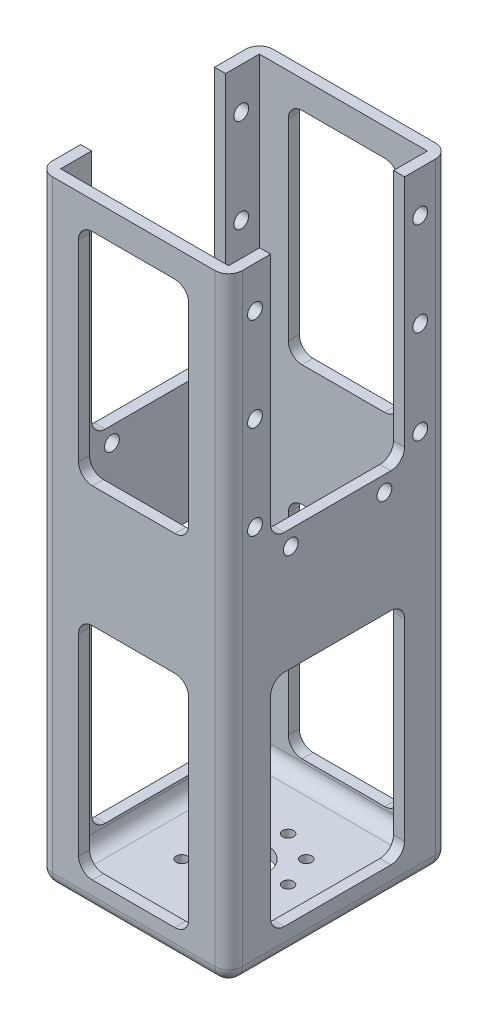
SolidWorks part; units mm, degrees
material "PLA"
ref_plane "Front Plane" through (0, 0, 0) normal (0, 0, 1) x (1, 0, 0)
ref_plane "Top Plane" through (0, 0, 0) normal (0, 1, 0) x (1, 0, 0)
ref_plane "Right Plane" through (0, 0, 0) normal (1, 0, 0) x (0, 0, -1)
other "Center of Mass"
sketch "Sketch1" plane through (0, 0, 0) normal (0, 1, 0) x (1, 0, 0)
  circle A0 centre (0, 0) radius 8 construction
  circle A1 centre (0, 8) radius 1
  circle A2 centre (5.6569, 5.6569) radius 1
  circle A3 centre (8, 0) radius 1
  circle A4 centre (5.6569, -5.6569) radius 1
  circle A5 centre (0, -8) radius 1
  circle A6 centre (-5.6569, -5.6569) radius 1
  circle A7 centre (-8, 0) radius 1
  circle A8 centre (-5.6569, 5.6569) radius 1
  circle A9 centre (0, 0) radius 4.25
  point P21 (0, 0)
  dimension "D1" = 16
  dimension "D2" = 2
  dimension "D4" = 8.5
  dimension "D3" = 8
sketch "Sketch2" plane through (0, 0, 0) normal (0, 1, 0) x (1, 0, 0)
  line L1 (-17.25, -20.05) -> (17.25, -20.05)
  line L2 (-17.25, -20.05) -> (-17.25, 20.05)
  line L3 (-17.25, 20.05) -> (17.25, 20.05)
  line L4 (17.25, -20.05) -> (17.25, 20.05)
  line L5 (-17.25, -20.05) -> (17.25, 20.05) construction
  line L6 (-17.25, 20.05) -> (17.25, -20.05) construction
  point P0 (0, 0)
  dimension "D1" = 34.5
  dimension "D2" = 40.1
extrude "Boss-Extrude1" add sketch "Sketch2" along normal blind 2
extrude "Cut-Extrude2" cut sketch "Sketch1" along normal through all
sketch "Sketch3" plane through (0, 2, 0) normal (0, 1, 0) x (1, 0, 0)
  line L5 (-17.25, -20.05) -> (17.25, -20.05) construction
  line L10 (17.25, -20.05) -> (17.25, 20.05) construction
  line L11 (17.25, 20.05) -> (-17.25, 20.05) construction
  line L12 (-17.25, 20.05) -> (-17.25, -20.05) construction
  line L13 (-17.25, -20.05) -> (17.25, -20.05)
  line L14 (17.25, -20.05) -> (17.25, 20.05)
  line L15 (17.25, 20.05) -> (-17.25, 20.05)
  line L16 (-17.25, 20.05) -> (-17.25, -20.05)
  line L17 (15.25, 18.05) -> (-15.25, 18.05)
  line L18 (-15.25, 18.05) -> (-15.25, -18.05)
  line L19 (-15.25, -18.05) -> (15.25, -18.05)
  line L20 (15.25, -18.05) -> (15.25, 18.05)
  dimension "D1" = 2
extrude "Boss-Extrude3" add sketch "Sketch3" along normal blind 110
sketch "Sketch4" plane through (-17.25, 0, 0) normal (-1, 0, 0) x (0, 0, 1)
  line L0 (-11.9182, 70) -> (-11.9182, 109)
  line L1 (-11.9182, 67) -> (-11.9182, 112)
  line L2 (12.4182, 109) -> (12.4182, 70)
  line L3 (12.4182, 112) -> (12.4182, 67)
  line L4 (-11.9182, 67) -> (12.4182, 67)
  line L6 (-11.9182, 112) -> (12.4182, 112)
  line L7 (-20.05, 112) -> (20.05, 112) construction
  line L8 (-20.05, 56) -> (20.05, 56) construction
  line L9 (-20.05, 112) -> (-20.05, 0) construction
  line L10 (20.05, 112) -> (20.05, 0) construction
  line L11 (-11.9182, 45) -> (12.4182, 45)
  line L12 (12.4182, 5) -> (12.4182, 45)
  line L13 (-11.9182, 45) -> (-11.9182, 5)
  line L14 (-11.9182, 5) -> (12.4182, 5)
  dimension "D1" = 45
  dimension "D2" = 40
extrude "Cut-Extrude3" cut sketch "Sketch4" against normal through all
sketch "Sketch5" plane through (0, 0, 20.05) normal (0, 0, 1) x (1, 0, 0)
  line L0 (0, 67) -> (0, 45) construction
  line L1 (-10, 5) -> (10, 5)
  line L2 (-10, 5) -> (-10, 45)
  line L3 (-10, 45) -> (10, 45)
  line L4 (10, 5) -> (10, 45)
  line L5 (-10, 5) -> (10, 45) construction
  line L6 (-10, 45) -> (10, 5) construction
  line L7 (-10, 67) -> (10, 67)
  line L8 (-10, 67) -> (-10, 107)
  line L9 (-10, 107) -> (10, 107)
  line L10 (10, 67) -> (10, 107)
  line L11 (-10, 67) -> (10, 107) construction
  line L12 (-10, 107) -> (10, 67) construction
  line L13 (0, 87) -> (0, 112) construction
  line L14 (-17.25, 112) -> (17.25, 112) construction
  line L15 (0, 0) -> (0, 25) construction
  line L16 (-17.25, 0) -> (17.25, 0) construction
  point P0 (0, 25)
  point P5 (0, 87)
  dimension "D1" = 25
  dimension "D2" = 25
  dimension "D3" = 40
  dimension "D4" = 20
extrude "Cut-Extrude4" cut sketch "Sketch5" against normal through all
fillet "Fillet1" radius 2.5 40 edges at (17.25, 56, 20.05) (-17.25, 56, -20.05) (0, 0, -20.05) (17.25, 56, -20.05) (17.25, 0, 0) (0, 0, 20.05) (-17.25, 56, 20.05) (-17.25, 0, 0) (0, 2, 18.05) (-15.25, 2, 0) (0, 2, -18.05) (15.25, 2, 0) (-10, 45, 19.05) (-10, 45, -19.05) (-10, 107, -19.05) (-10, 107, 19.05) (10, 107, 19.05) (10, 107, -19.05) (10, 45, -19.05) (10, 45, 19.05) (-10, 67, 19.05) (10, 67, 19.05) (10, 67, -19.05) (-10, 67, -19.05) (-10, 5, -19.05) (10, 5, -19.05) (-10, 5, 19.05) (10, 5, 19.05) (-16.25, 67, 12.4182) (-16.25, 67, -11.9182) (16.25, 67, -11.9182) (16.25, 67, 12.4182) (16.25, 45, -11.9182) (-16.25, 45, -11.9182) (16.25, 45, 12.4182) (-16.25, 45, 12.4182) (-16.25, 5, 12.4182) (16.25, 5, 12.4182) (16.25, 5, -11.9182) (-16.25, 5, -11.9182)
sketch "Sketch7" plane through (-17.25, 0, 0) normal (-1, 0, 0) x (0, 0, 1)
  line L0 (-17.55, 112) -> (-11.9182, 112) construction
  line L1 (-14.75, 104.5) -> (-14.75, 70.5) construction
  line L2 (15.25, 104.5) -> (15.25, 112) construction
  line L3 (-11.9182, 112) -> (-11.9182, 69.5) construction
  line L4 (-14.75, 70.5) -> (-14.75, 64.2) construction
  line L5 (-14.75, 64.2) -> (15.25, 64.2) construction
  line L6 (15.25, 64.2) -> (15.25, 104.5) construction
  line L10 (12.4182, 112) -> (17.55, 112) construction
  circle A0 centre (-14.75, 104.5) radius 1.35
  circle A1 centre (-14.75, 87.5) radius 1.35
  circle A2 centre (-14.75, 70.5) radius 1.35
  circle A3 centre (15.25, 104.5) radius 1.35
  circle A4 centre (15.25, 87.5) radius 1.35
  circle A5 centre (15.25, 70.5) radius 1.35
  circle A6 centre (-8.25, 64.2) radius 1.35
  circle A7 centre (8.75, 64.2) radius 1.35
  point P8 (0, 0)
  point P11 (0, 0)
  point P14 (0, 0)
  point P17 (0, 0)
  point P20 (0, 0)
  point P23 (0, 0)
  point P29 (0, 0)
  point P30 (0, 0)
  point P31 (0, 0)
  point P32 (0, 0)
  dimension "D1" = 2.7
  dimension "D2" = 2.7
  dimension "D3" = 2.7
  dimension "D4" = 2.7
  dimension "D5" = 2.7
  dimension "D6" = 2.7
  dimension "D7" = 2.7
  dimension "D8" = 2.7
  dimension "D15" = 17
  dimension "D16" = 6.5
  dimension "D17" = 6.5
  dimension "D18" = 6.3
  dimension "D19" = 17
  dimension "D20" = 17
  dimension "D9" = 7.5
  dimension "D10" = 17
  dimension "D11" = 2.8318
  dimension "D12" = 17
  dimension "D13" = 6.3
  dimension "D14" = 30
extrude "Cut-Extrude5" cut sketch "Sketch7" against normal through all
